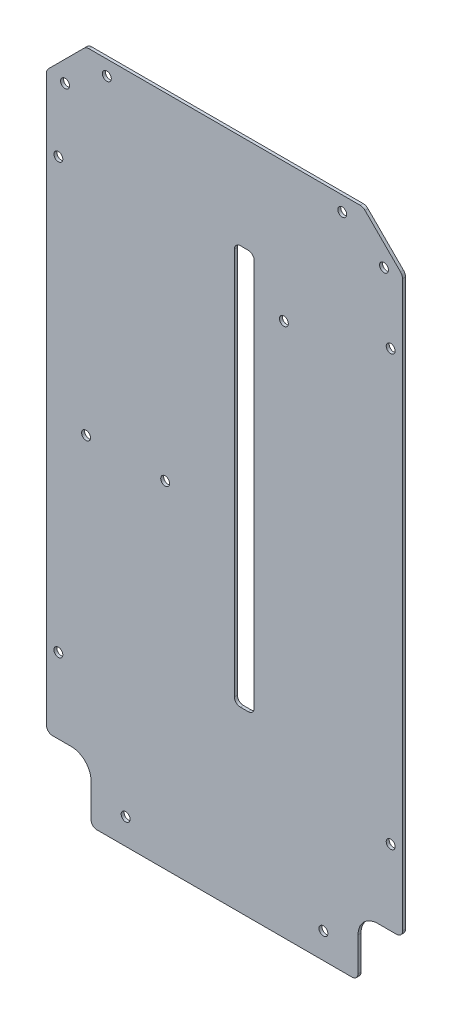
SolidWorks part; units mm, degrees
material "1023 Tôle d'acier au carbone (SS)"
ref_plane "Plan de face" through (0, 0, 0) normal (0, 0, 1) x (1, 0, 0)
ref_plane "Plan de dessus" through (0, 0, 0) normal (0, 1, 0) x (1, 0, 0)
ref_plane "Plan de droite" through (0, 0, 0) normal (1, 0, 0) x (0, 0, -1)
sketch "Esquisse1" plane through (0, 0, 0) normal (0, 0, 1) x (1, 0, 0)
  line L1 (0, 0) -> (180, 0)
  line L2 (0, 0) -> (0, 340)
  line L3 (0, 340) -> (180, 340)
  line L4 (180, 0) -> (180, 340)
  dimension "D1" = 180
  dimension "D2" = 340
extrude "Boss.-Extru.1" add sketch "Esquisse1" along normal blind 1.5
sketch "Esquisse2" plane through (0, 0, 1.5) normal (0, 0, 1) x (1, 0, 0)
  line L0 (0, 13) -> (180, 13) construction
  line L1 (0, 340) -> (0, 0) construction
  line L2 (180, 0) -> (180, 340) construction
  line L3 (0, 0) -> (180, 0) construction
  circle A0 centre (40, 13) radius 2.25
  circle A1 centre (140, 13) radius 2.25
  dimension "D1" = 4.5
  dimension "D3" = 40
  dimension "D4" = 100
  dimension "D2" = 13
extrude "Enlèv. mat.-Extru.1" cut sketch "Esquisse2" against normal through all both and the other way through all
sketch "Esquisse3" plane through (0, 0, 1.5) normal (0, 0, 1) x (1, 0, 0)
  line L1 (0, 0) -> (22.5, 0)
  line L2 (0, 0) -> (0, 30)
  line L3 (0, 30) -> (22.5, 30)
  line L4 (22.5, 0) -> (22.5, 30)
  line L5 (180, 0) -> (157.5, 0)
  line L6 (180, 0) -> (180, 30)
  line L7 (180, 30) -> (157.5, 30)
  line L8 (157.5, 0) -> (157.5, 30)
  dimension "D1" = 30
  dimension "D2" = 22.5
  dimension "D3" = 22.5
extrude "Enlèv. mat.-Extru.2" cut sketch "Esquisse3" against normal through all both and the other way through all
fillet "Congé1" radius 10 2 edges at (157.5, 30, 0.75) (22.5, 30, 0.75)
fillet "Congé2" radius 3 4 edges at (0, 30, 0.75) (22.5, 0, 0.75) (180, 30, 0.75) (157.5, 0, 0.75)
sketch "Esquisse4" plane through (0, 0, 1.5) normal (0, 0, 1) x (1, 0, 0)
  line L0 (0, 340) -> (0, 33) construction
  line L1 (95, 292) -> (105, 292)
  line L2 (95, 292) -> (95, 90)
  line L3 (95, 90) -> (105, 90)
  line L4 (105, 292) -> (105, 90)
  line L5 (25.5, 0) -> (154.5, 0) construction
  dimension "D1" = 95
  dimension "D2" = 10
  dimension "D3" = 90
  dimension "D4" = 202
extrude "Enlèv. mat.-Extru.3" cut sketch "Esquisse4" against normal through all both and the other way through all
fillet "Congé3" radius 3 4 edges at (95, 292, 0.75) (105, 292, 0.75) (105, 90, 0.75) (95, 90, 0.75)
chamfer "Chanfrein1" distance 20 angle 45 1 edges at (180, 340, 0.75)
chamfer "Chanfrein2" distance 20 angle 45 1 edges at (0, 340, 0.75)
sketch "Esquisse5" plane through (0, 0, 1.5) normal (0, 0, 1) x (1, 0, 0)
  line L0 (180, 270) -> (120, 270) construction
  line L1 (180, 33) -> (180, 320) construction
  line L2 (25.5, 0) -> (154.5, 0) construction
  circle A0 centre (120, 270) radius 2.25
  dimension "D2" = 4.5
  dimension "D1" = 60
  dimension "D3" = 270
extrude "Enlèv. mat.-Extru.4" cut sketch "Esquisse5" against normal through all
sketch "Esquisse6" plane through (0, 0, 1.5) normal (0, 0, 1) x (1, 0, 0)
  line L0 (6, 0) -> (6, 285) construction
  line L1 (0, 320) -> (0, 33) construction
  line L2 (6, 0) -> (0, 0) construction
  line L3 (0, 176.5) -> (180, 176.5) construction
  line L4 (180, 33) -> (180, 320) construction
  line L5 (90, 176.5) -> (90, -87.4402) construction
  line L6 (20, 170) -> (60, 170) construction
  line L7 (25.5, 0) -> (154.5, 0) construction
  line L8 (170.6308, 318.7626) -> (175.9341, 324.0659) construction
  line L9 (160, 340) -> (20, 340) construction
  line L10 (180, 320) -> (160, 340) construction
  line L11 (149.5, 332.5) -> (149.5, 340) construction
  line L12 (90, 340) -> (90, 301.4334) construction
  line L13 (30.5, 332.5) -> (30.5, 340) construction
  line L14 (9.3692, 318.7626) -> (4.0659, 324.0659) construction
  circle A0 centre (6, 285) radius 2.25
  circle A1 centre (6, 68) radius 2.25
  circle A2 centre (174, 68) radius 2.25
  circle A3 centre (174, 285) radius 2.25
  circle A4 centre (20, 170) radius 2.25
  circle A5 centre (60, 170) radius 2.25
  circle A6 centre (149.5, 332.5) radius 2.25
  circle A7 centre (170.6308, 318.7626) radius 2.25
  circle A8 centre (9.3692, 318.7626) radius 2.25
  circle A9 centre (30.5, 332.5) radius 2.25
  dimension "D1" = 4.5
  dimension "D4" = 68
  dimension "D5" = 40
  dimension "D6" = 20
  dimension "D10" = 10.5
  dimension "D11" = 5.75
  dimension "D2" = 285
  dimension "D3" = 6
  dimension "D7" = 170
  dimension "D8" = 7.5
  dimension "D9" = 7.5
extrude "Enlèv. mat.-Extru.5" cut sketch "Esquisse6" against normal through all both and the other way through all
fillet "Congé4" radius 3.5 4 edges at (180, 320, 0.75) (160, 340, 0.75) (20, 340, 0.75) (0, 320, 0.75)
